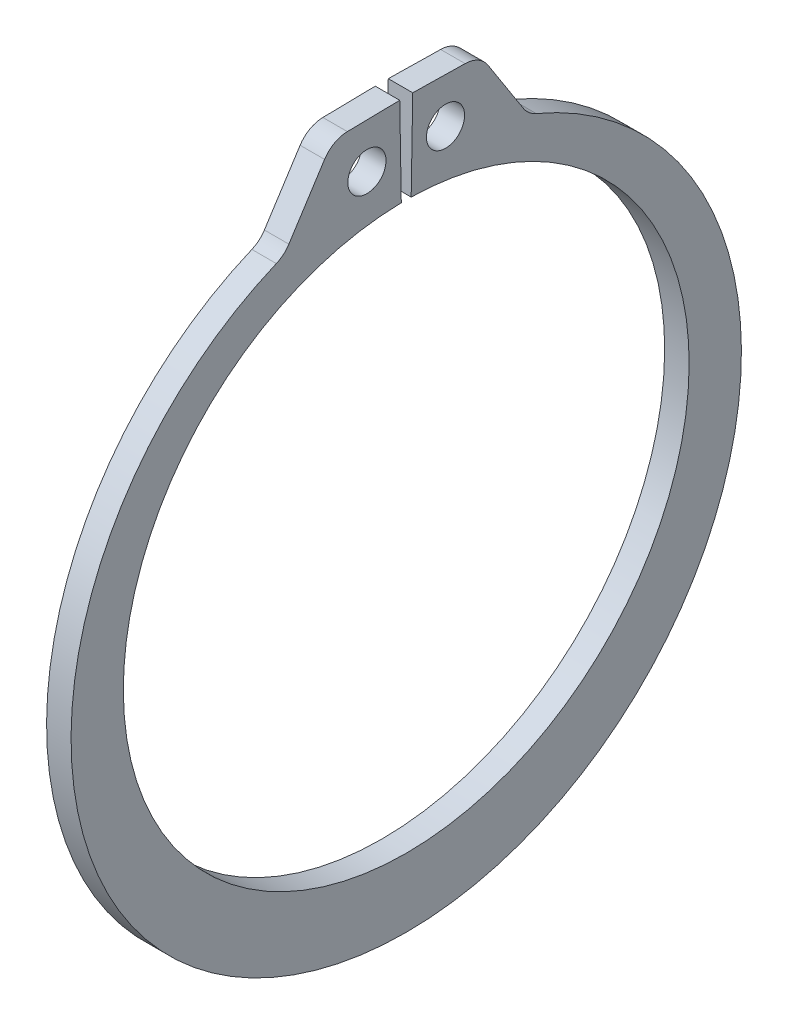
SolidWorks part; units mm, degrees
material "Cast Carbon Steel"
ref_plane "Front" through (0, 0, 0) normal (0, 0, 1) x (1, 0, 0)
ref_plane "Top" through (0, 0, 0) normal (0, 1, 0) x (1, 0, 0)
ref_plane "Right" through (0, 0, 0) normal (1, 0, 0) x (0, 0, -1)
sketch "Sketch1" plane through (0, 0, 0) normal (1, 0, 0) x (0, 0, -1)
  line L0 (0, 0) -> (0, 14.6812) construction
  line L1 (-0.2562, 14.679) -> (-0.3373, 19.3265)
  line L2 (0.3373, 19.3265) -> (3.823, 19.2656)
  line L3 (3.823, 19.2656) -> (6.3364, 15.3556)
  line L4 (0.2562, 14.679) -> (0.3373, 19.3265)
  line L5 (-0.3373, 19.3265) -> (-3.823, 19.2656)
  line L6 (-3.823, 19.2656) -> (-6.3364, 15.3556)
  line L7 (-6.3364, 15.3556) -> (-5.6001, 13.5712) construction
  line L8 (6.3364, 15.3556) -> (5.6001, 13.5712) construction
  line L9 (0, -14.6812) -> (0, -18.2372) construction
  line L10 (-3.823, 19.2656) -> (-0.2562, 14.679) construction
  line L11 (0, 14.6812) -> (0, 19.3294) construction
  line L12 (-14.6812, 0) -> (14.6812, 0) construction
  circle A0 centre (0, 0) radius 14.6812 construction
  arc A1 (-0.2562, 14.679) -> (0.2562, 14.679) centre (0, 0) ccw
  circle A3 centre (0, 0) radius 21.0185 construction
  circle A4 centre (-2.0396, 16.9723) radius 0.9906
  circle A5 centre (2.0396, 16.9723) radius 0.9906
  arc A6 (-6.3364, 15.3556) -> (6.3364, 15.3556) centre (0, -0.8432) ccw
  point P0 (0, -18.2372)
  dimension "A" = 29.3624
  dimension "Hole" = 1.9812
  dimension "Smin" = 1.9304
  dimension "H" = 4.6482
  dimension "D2" = 3.4861
  dimension "Angle" = 1
extrude "Extrude1" add sketch "Sketch1" along normal mid plane 1.27
fillet "Fillet1" radius 1.4351 4 edges at (0, 15.3556, 6.3364) (0, 15.3556, -6.3364) (0, 19.2656, 3.823) (0, 19.2656, -3.823)
sketch "Sketch2" plane through (0, 0, 0) normal (0, 0, 1) x (1, 0, 0)
  line L0 (-7.0612, 0) -> (18.3388, 0)
  line L1 (18.3388, 0) -> (18.3388, -15.875)
  line L2 (-0.7112, -15.875) -> (-6.1214, -15.875)
  line L3 (18.3388, -15.875) -> (0.7112, -15.875)
  line L4 (0.7112, -15.875) -> (0.7112, -14.9352)
  line L5 (0.7112, -14.9352) -> (-0.7112, -14.9352)
  line L6 (-0.7112, -14.9352) -> (-0.7112, -15.875)
  line L7 (-0.7112, -15.875) -> (-7.0612, -15.875) construction
  line L8 (-7.0612, -15.875) -> (-7.0612, 0) construction
  line L9 (18.3388, 0) -> (76.391, 0) construction
  line L10 (-6.1214, -15.875) -> (-7.0612, -14.9352)
  line L11 (-7.0612, -14.9352) -> (-7.0612, 0)
  point P10 (0, -14.9352)
  dimension "D2" = 25.4
  dimension "D3" = 6.35
  dimension "D1" = 45
revolve "Revolve1" [suppressed] add sketch "Sketch2" angle 360 about L9
delete or keep bodies "Body-Delete1" [suppressed] type delete bodies bodies 122
equation "\"D2@Sketch2\" = \"D1@Extrude1\"*20"
equation "\"D3@Sketch2\" = \"D2@Sketch2\"/4"
equation "\"D2@Sketch1\" = \"H@Sketch1\"*.75"
